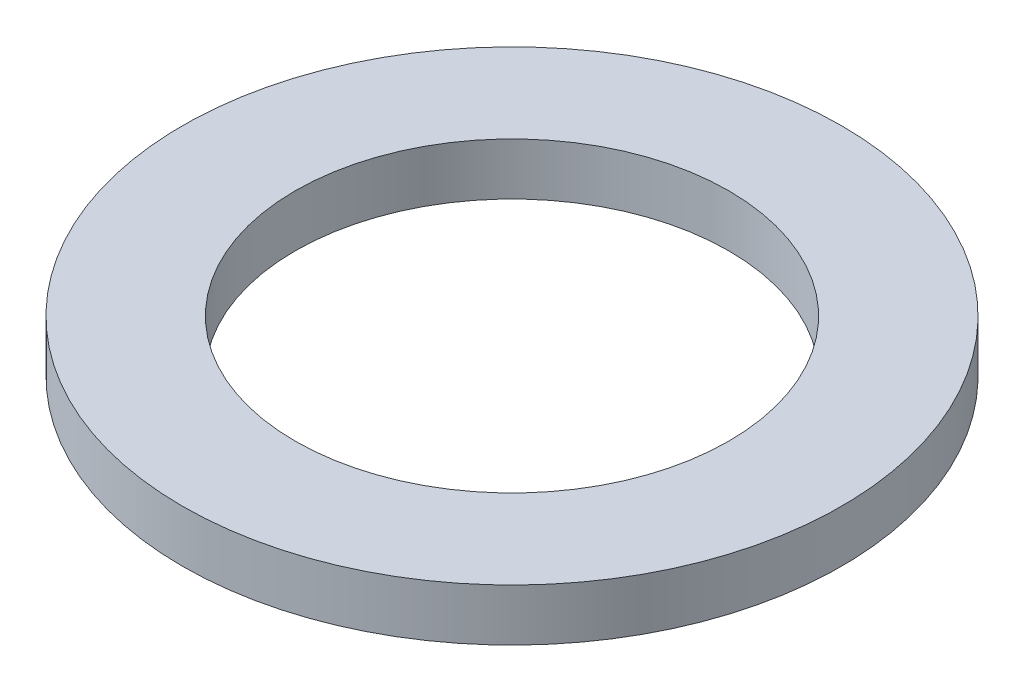
SolidWorks part; units mm, degrees
material "1.0037 (S235JR)"
ref_plane "Front Plane" through (0, 0, 0) normal (0, 0, 1) x (1, 0, 0)
ref_plane "Top Plane" through (0, 0, 0) normal (0, 1, 0) x (1, 0, 0)
ref_plane "Right Plane" through (0, 0, 0) normal (1, 0, 0) x (0, 0, -1)
sketch "Sketch1" plane through (0, 0, 0) normal (0, 1, 0) x (1, 0, 0)
  circle A0 centre (0, 0) radius 19
  circle A1 centre (0, 0) radius 12.5
  dimension "D1" = 38
  dimension "D2" = 25
extrude "Boss-Extrude1" add sketch "Sketch1" along normal blind 3
